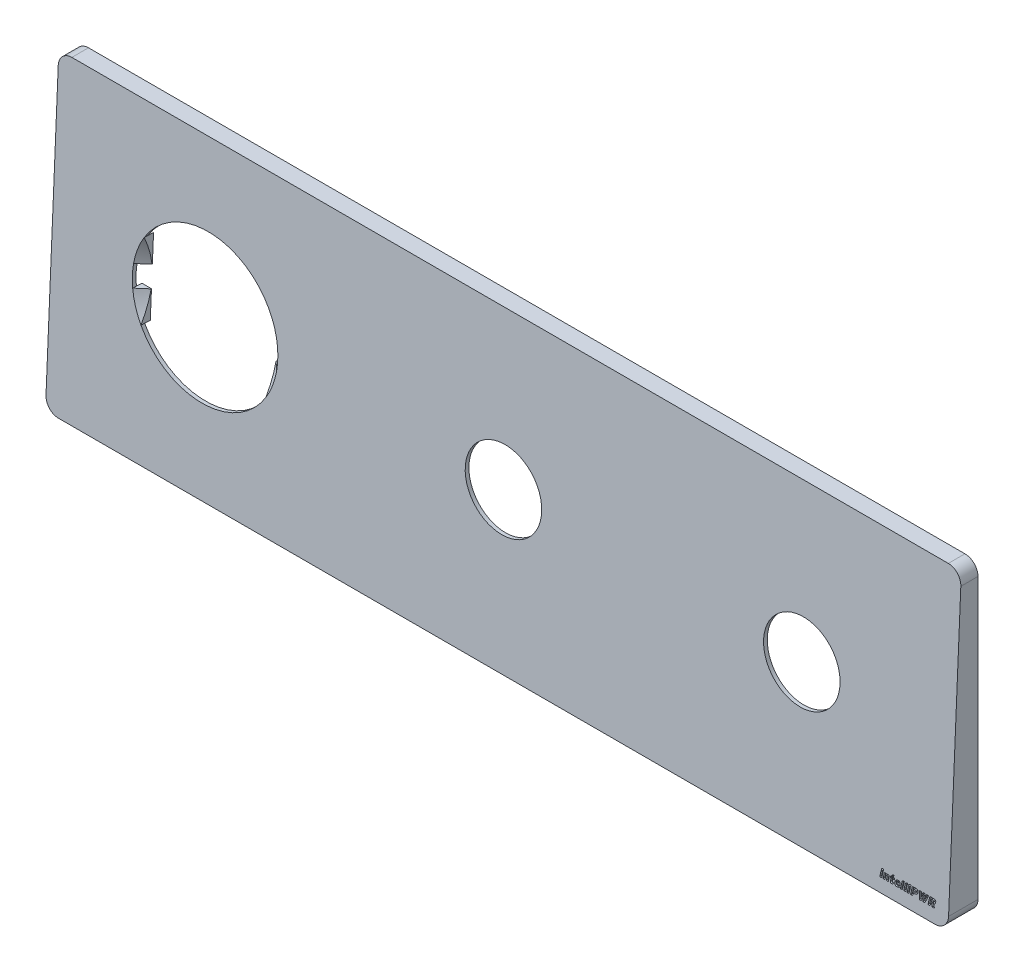
SolidWorks part; units mm, degrees
ref_plane "Front Plane" through (0, 0, 0) normal (0, 0, 1) x (1, 0, 0)
ref_plane "Top Plane" through (0, 0, 0) normal (0, 1, 0) x (1, 0, 0)
ref_plane "Right Plane" through (0, 0, 0) normal (1, 0, 0) x (0, 0, -1)
sketch "Sketch1" plane through (0, 0, 0) normal (0, 0, 1) x (1, 0, 0)
  line L0 (-38.566, 0) -> (72.4153, 0) construction
  line L1 (0, -49.5581) -> (0, 74.5126) construction
  line L2 (-37.5, 40) -> (197.5, 40)
  line L3 (-40, 37.5) -> (-40, -37.5)
  line L4 (-37.5, -40) -> (197.5, -40)
  line L5 (200, 37.5) -> (200, -37.5)
  arc A0 (-40, -37.5) -> (-37.5, -40) centre (-37.5, -37.5) ccw
  arc A1 (197.5, -40) -> (200, -37.5) centre (197.5, -37.5) ccw
  arc A2 (197.5, 40) -> (200, 37.5) centre (197.5, 37.5) cw
  arc A3 (-37.5, 40) -> (-40, 37.5) centre (-37.5, 37.5) ccw
  dimension "D3" = 2.5
  dimension "D1" = 240
  dimension "D2" = 80
  dimension "D4" = 40
  dimension "D5" = 40
extrude "Extrude-Thin1" add sketch "Sketch1" along normal blind 8 thin thin type one direction wall 1
sketch "Sketch5" plane through (201, 0, 0) normal (1, 0, 0) x (0, 0, -1)
  line L0 (20.3178, 0) -> (-25.0092, 0) construction
  line L1 (0, 43.59) -> (0, -45.2443) construction
  line L2 (-3.4562, 41) -> (-8, 41)
  line L3 (-8, 41) -> (-8, -41)
  line L4 (-8, -41) -> (-7.0437, -41)
  line L6 (-7.0437, -41) -> (-3.4562, 41)
  line L7 (-8, -41) -> (0, -41) construction
  line L11 (-8, 41) -> (0, 41) construction
extrude "Cut-Extrude2" cut sketch "Sketch5" against normal blind 242
sketch "Sketch6" plane through (201, 0, 0) normal (1, 0, 0) x (0, 0, -1)
  line L0 (-7.0437, -41) -> (-3.4562, 41)
  line L1 (-3.4562, 41) -> (-4.4572, 41)
  line L2 (-4.4572, 41) -> (-8.0447, -41)
  line L3 (-8.0447, -41) -> (-7.0437, -41)
  line L4 (-3.4562, 41) -> (-3.4562, 45.0301) construction
  dimension "D1" = 1
  dimension "D2" = 90
extrude "Boss-Extrude1" add sketch "Sketch6" against normal blind 242
sketch "Sketch7" plane through (0, 0, 0) normal (0, 0, -1) x (-1, 0, 0)
  line L0 (-201, 37.5) -> (-201, 41)
  line L1 (-201, 41) -> (-197.5, 41)
  line L2 (-18.5365, 0) -> (-146.383, 0) construction
  line L3 (-80, 24.4375) -> (-80, -25.4386) construction
  line L5 (41, 41) -> (37.5, 41)
  line L6 (41, 37.5) -> (41, 41)
  line L7 (41, -37.5) -> (41, -41)
  line L8 (41, -41) -> (37.5, -41)
  line L9 (-201, -41) -> (-197.5, -41)
  line L10 (-201, -37.5) -> (-201, -41)
  arc A0 (-197.5, 41) -> (-201, 37.5) centre (-197.5, 37.5) ccw
  arc A1 (37.5, 41) -> (41, 37.5) centre (37.5, 37.5) cw
  arc A2 (37.5, -41) -> (41, -37.5) centre (37.5, -37.5) ccw
  arc A3 (-197.5, -41) -> (-201, -37.5) centre (-197.5, -37.5) cw
sketch "Sketch8" plane through (0, 0.273, 6.239) normal (0, 0.0437, 0.999) x (1, 0, 0)
  line L0 (0, 0) -> (0, 28.9526) construction
  line L1 (23.1598, 0) -> (-27.4609, 0) construction
  circle A0 centre (0, 0) radius 19.5
  dimension "D1" = 39
extrude "Kes-Ekstrüzyon5" cut sketch "Sketch7" against normal blind 10
extrude "Cut-Extrude3" cut sketch "Sketch8" against normal blind 82
sketch "Sketch9" plane through (0, 0.273, 6.239) normal (0, 0.0437, 0.999) x (1, 0, 0)
  line L1 (182.5318, -37.8124) -> (182.8563, -36.2774)
  line L3 (182.8563, -36.2774) -> (183.3824, -36.2774)
  line L4 (183.3824, -36.2774) -> (183.058, -37.8124)
  line L5 (183.058, -37.8124) -> (182.5318, -37.8124)
  line L6 (184.2906, -37.8124) -> (184.4746, -36.9301)
  line L7 (184.121, -36.9242) -> (183.9366, -37.8124)
  line L8 (183.9366, -37.8124) -> (183.4104, -37.8124)
  line L9 (183.4104, -37.8124) -> (183.7348, -36.2694)
  line L10 (183.7348, -36.2694) -> (184.261, -36.2694)
  line L11 (184.261, -36.2694) -> (184.2407, -36.3734)
  line L12 (185.0186, -36.8721) -> (184.8197, -37.8124)
  line L13 (184.8197, -37.8124) -> (184.2906, -37.8124)
  line L14 (185.3946, -37.3472) -> (185.5346, -36.6755)
  line L15 (185.5346, -36.6755) -> (185.3007, -36.6755)
  line L16 (185.3007, -36.6755) -> (185.3887, -36.2694)
  line L17 (185.3887, -36.2694) -> (185.6226, -36.2694)
  line L18 (185.6226, -36.2694) -> (185.7042, -35.8811)
  line L19 (185.7042, -35.8811) -> (186.2596, -35.6738)
  line L20 (186.2596, -35.6738) -> (186.134, -36.2694)
  line L21 (186.134, -36.2694) -> (186.4673, -36.2694)
  line L22 (186.4673, -36.2694) -> (186.3797, -36.6755)
  line L23 (186.3797, -36.6755) -> (186.0464, -36.6755)
  line L24 (186.0464, -36.6755) -> (185.9292, -37.2389)
  line L25 (186.2571, -37.3099) -> (186.0929, -37.7574)
  line L26 (187.0891, -36.865) -> (187.5277, -36.865)
  line L27 (187.9194, -37.1898) -> (187.0193, -37.1898)
  line L28 (187.6478, -37.3252) -> (187.7794, -37.6631)
  line L29 (188.0814, -37.8124) -> (188.4875, -35.8849)
  line L30 (188.4875, -35.8849) -> (189.0576, -35.6738)
  line L31 (189.0576, -35.6738) -> (188.6076, -37.8124)
  line L32 (188.6076, -37.8124) -> (188.0814, -37.8124)
  line L33 (188.9747, -37.8124) -> (189.3808, -35.8849)
  line L34 (189.3808, -35.8849) -> (189.951, -35.6738)
  line L35 (189.951, -35.6738) -> (189.5009, -37.8124)
  line L36 (189.5009, -37.8124) -> (188.9747, -37.8124)
  line L37 (189.8681, -37.8124) -> (190.1925, -36.2774)
  line L38 (190.1925, -36.2774) -> (190.7187, -36.2774)
  line L39 (190.7187, -36.2774) -> (190.3943, -37.8124)
  line L40 (190.3943, -37.8124) -> (189.8681, -37.8124)
  line L41 (191.9923, -36.2152) -> (191.6852, -36.2152)
  line L42 (191.6852, -36.2152) -> (191.5858, -36.6755)
  line L43 (191.5858, -36.6755) -> (191.884, -36.6755)
  line L44 (191.7728, -37.1357) -> (191.4894, -37.1357)
  line L45 (191.4894, -37.1357) -> (191.3489, -37.8124)
  line L46 (191.3489, -37.8124) -> (190.7906, -37.8124)
  line L47 (190.7906, -37.8124) -> (191.2233, -35.755)
  line L48 (191.2233, -35.755) -> (192.1031, -35.755)
  line L49 (194.6592, -37.8124) -> (194.1292, -37.8124)
  line L50 (194.1292, -37.8124) -> (194.1292, -37.3658)
  line L51 (193.8492, -37.3658) -> (193.6618, -37.8124)
  line L52 (193.6618, -37.8124) -> (193.1445, -37.8124)
  line L53 (193.1445, -37.8124) -> (193.0891, -35.755)
  line L54 (193.0891, -35.755) -> (193.6737, -35.755)
  line L55 (193.6737, -35.755) -> (193.6563, -36.0989)
  line L56 (193.9309, -36.1019) -> (194.0742, -35.755)
  line L57 (194.0742, -35.755) -> (194.6004, -35.755)
  line L58 (194.6004, -35.755) -> (194.5975, -36.1019)
  line L59 (194.8724, -36.0989) -> (195.001, -35.755)
  line L60 (195.001, -35.755) -> (195.5801, -35.755)
  line L61 (195.5801, -35.755) -> (194.6592, -37.8124)
  line L62 (196.7107, -36.2152) -> (196.3685, -36.2152)
  line L63 (196.3685, -36.2152) -> (196.2721, -36.6755)
  line L64 (196.2721, -36.6755) -> (196.6054, -36.6755)
  line L65 (196.5935, -37.8124) -> (196.4066, -37.1357)
  line L66 (196.4066, -37.1357) -> (196.1786, -37.1357)
  line L67 (196.1786, -37.1357) -> (196.0322, -37.8124)
  line L68 (196.0322, -37.8124) -> (195.4739, -37.8124)
  line L69 (195.4739, -37.8124) -> (195.9066, -35.755)
  line L70 (195.9066, -35.755) -> (196.8215, -35.755)
  line L71 (196.9823, -37.0278) -> (197.228, -37.8124)
  line L72 (197.228, -37.8124) -> (196.5935, -37.8124)
  spline S0 degree 3 poles (183.5051, -35.901) (183.4969, -35.9395) (183.475, -35.9951) (183.4259, -36.0567) (183.38, -36.0941) (183.3281, -36.1243) (183.2494, -36.1531) (183.1859, -36.1615) (183.1426, -36.1611) knots 0 0 0 0 0.243996 0.362518 0.483924 0.60781 0.732572 1 1 1 1
  spline S1 degree 3 poles (183.1426, -36.1611) (183.1034, -36.1614) (183.0464, -36.1543) (182.9794, -36.1247) (182.9459, -36.0992) (182.9246, -36.0749) (182.9109, -36.0553) (182.9015, -36.0333) (182.894, -36.0101) (182.8904, -35.985) (182.8893, -35.9483) (182.8933, -35.92) (182.8973, -35.901) knots 0 0 0 0 0.278361 0.398909 0.514848 0.572098 0.627439 0.683254 0.740687 0.799243 0.862128 1 1 1 1
  spline S2 degree 3 poles (182.8973, -35.901) (182.9046, -35.8648) (182.9269, -35.8129) (182.975, -35.7545) (183.0208, -35.7171) (183.0729, -35.6861) (183.1494, -35.6544) (183.2122, -35.6474) (183.2539, -35.6468) knots 0 0 0 0 0.233169 0.351346 0.477078 0.606225 0.734605 1 1 1 1
  spline S3 degree 3 poles (183.2539, -35.6468) (183.294, -35.6476) (183.3536, -35.6526) (183.4215, -35.6852) (183.4549, -35.7118) (183.4756, -35.7369) (183.4893, -35.7563) (183.4986, -35.7777) (183.5062, -35.8) (183.5103, -35.8237) (183.5118, -35.8577) (183.5094, -35.8837) (183.5051, -35.901) knots 0 0 0 0 0.289932 0.415109 0.533191 0.591068 0.646913 0.702321 0.757398 0.814668 0.873138 1 1 1 1
  spline S4 degree 3 poles (184.4746, -36.9301) (184.4788, -36.907) (184.4857, -36.8741) (184.4892, -36.8319) (184.4898, -36.805) (184.4882, -36.7812) (184.4845, -36.7603) (184.4788, -36.7423) (184.4679, -36.723) (184.4497, -36.7035) (184.4108, -36.6804) (184.3757, -36.6755) (184.3519, -36.6755) knots 0 0 0 0 0.206248 0.294568 0.372668 0.442258 0.50401 0.558886 0.607164 0.698385 0.78958 1 1 1 1
  spline S5 degree 3 poles (184.3519, -36.6755) (184.3255, -36.6748) (184.2865, -36.6813) (184.2396, -36.7028) (184.2139, -36.7214) (184.195, -36.7398) (184.1826, -36.7576) (184.1702, -36.7778) (184.159, -36.8014) (184.1478, -36.8274) (184.1346, -36.8686) (184.1258, -36.9012) (184.121, -36.9242) knots 0 0 0 0 0.211446 0.310999 0.411311 0.464021 0.521401 0.584742 0.653943 0.729878 0.812026 1 1 1 1
  spline S6 degree 3 poles (184.2407, -36.3734) (184.298, -36.3381) (184.3731, -36.2966) (184.4716, -36.2624) (184.5492, -36.2465) (184.6106, -36.2424) (184.6531, -36.2423) knots 0 0 0 0 0.460544 0.581348 0.71025 1 1 1 1
  spline S7 degree 3 poles (184.6531, -36.2423) (184.6921, -36.2424) (184.7488, -36.2462) (184.8195, -36.2639) (184.8654, -36.2813) (184.9061, -36.3046) (184.9414, -36.333) (184.9715, -36.3666) (184.9962, -36.4051) (185.0154, -36.4485) (185.031, -36.4959) (185.0401, -36.5481) (185.0459, -36.6044) (185.0457, -36.6652) (185.0409, -36.7555) (185.0276, -36.8247) (185.0186, -36.8721) knots 0 0 0 0 0.133988 0.193276 0.249258 0.301629 0.353161 0.403793 0.455519 0.509135 0.565969 0.625946 0.690505 0.759591 0.834116 1 1 1 1
  spline S8 degree 3 poles (186.0929, -37.7574) (186.0333, -37.7837) (185.9543, -37.8089) (185.856, -37.8278) (185.7854, -37.8368) (185.7316, -37.8398) (185.6953, -37.8395) knots 0 0 0 0 0.477931 0.605354 0.733676 1 1 1 1
  spline S9 degree 3 poles (185.6953, -37.8395) (185.6631, -37.8397) (185.6164, -37.8366) (185.5579, -37.8244) (185.5198, -37.8123) (185.4862, -37.7963) (185.457, -37.7764) (185.4315, -37.7536) (185.4109, -37.7263) (185.3947, -37.6948) (185.3825, -37.6588) (185.3741, -37.6184) (185.3701, -37.5731) (185.3704, -37.5232) (185.3757, -37.4469) (185.3864, -37.3879) (185.3946, -37.3472) knots 0 0 0 0 0.137072 0.197692 0.25376 0.30627 0.355446 0.403354 0.450795 0.500091 0.55332 0.611471 0.675246 0.745926 0.823384 1 1 1 1
  spline S10 degree 3 poles (185.9292, -37.2389) (185.9236, -37.2632) (185.9182, -37.2972) (185.9231, -37.3387) (185.9338, -37.3601) (185.9509, -37.3746) (185.9818, -37.3894) (186.0096, -37.391) (186.0286, -37.3916) knots 0 0 0 0 0.332431 0.451864 0.549009 0.641836 0.743993 1 1 1 1
  spline S11 degree 3 poles (186.0286, -37.3916) (186.0648, -37.392) (186.1102, -37.3818) (186.1624, -37.3596) (186.204, -37.3401) (186.2353, -37.3223) (186.2571, -37.3099) knots 0 0 0 0 0.439023 0.560347 0.693744 1 1 1 1
  spline S12 degree 3 poles (187.5277, -36.865) (187.5293, -36.8295) (187.529, -36.7789) (187.5142, -36.7178) (187.5009, -36.6876) (187.4872, -36.6673) (187.4736, -36.6552) (187.4583, -36.6443) (187.44, -36.6359) (187.4195, -36.6292) (187.3871, -36.6229) (187.3615, -36.621) (187.3437, -36.6213) knots 0 0 0 0 0.296749 0.416695 0.521302 0.57019 0.620056 0.671542 0.726187 0.786738 0.851475 1 1 1 1
  spline S13 degree 3 poles (187.3437, -36.6213) (187.3155, -36.6212) (187.2732, -36.6284) (187.2232, -36.6548) (187.1894, -36.682) (187.1587, -36.7168) (187.1208, -36.7764) (187.1008, -36.8283) (187.0891, -36.865) knots 0 0 0 0 0.222963 0.331063 0.443598 0.564297 0.695588 1 1 1 1
  spline S14 degree 3 poles (187.946, -37.0879) (187.9408, -37.1068) (187.9333, -37.1411) (187.9259, -37.1755) (187.9194, -37.1898) knots 0 0 0 0 0.556454 1 1 1 1
  spline S15 degree 3 poles (187.0193, -37.1898) (187.0159, -37.2265) (187.016, -37.2792) (187.0367, -37.342) (187.0613, -37.3767) (187.0938, -37.4024) (187.1478, -37.4284) (187.1948, -37.4328) (187.2265, -37.4334) knots 0 0 0 0 0.296056 0.414656 0.524028 0.631631 0.743271 1 1 1 1
  spline S16 degree 3 poles (187.2265, -37.4334) (187.2603, -37.4332) (187.3107, -37.4303) (187.3768, -37.4199) (187.4263, -37.4095) (187.477, -37.3938) (187.5522, -37.3685) (187.6086, -37.3424) (187.6478, -37.3252) knots 0 0 0 0 0.230948 0.344109 0.457558 0.576208 0.706686 1 1 1 1
  spline S17 degree 3 poles (187.7794, -37.6631) (187.7271, -37.6911) (187.6473, -37.7284) (187.5385, -37.7689) (187.4578, -37.7948) (187.3756, -37.8147) (187.2619, -37.8343) (187.1745, -37.8392) (187.1157, -37.8395) knots 0 0 0 0 0.256454 0.380104 0.501569 0.622664 0.745735 1 1 1 1
  spline S18 degree 3 poles (187.1157, -37.8395) (187.0622, -37.8393) (186.9842, -37.8333) (186.8864, -37.8083) (186.822, -37.7829) (186.7641, -37.7507) (186.7129, -37.7122) (186.6679, -37.6684) (186.6299, -37.6183) (186.5991, -37.5624) (186.5744, -37.5016) (186.5568, -37.4353) (186.5454, -37.3642) (186.541, -37.2886) (186.5441, -37.1801) (186.5568, -37.0976) (186.5688, -37.0422) knots 0 0 0 0 0.139839 0.202933 0.262718 0.320042 0.375234 0.429353 0.483442 0.538621 0.595401 0.654489 0.717096 0.783083 0.851913 1 1 1 1
  spline S19 degree 3 poles (186.5688, -37.0422) (186.5831, -36.9792) (186.6085, -36.8876) (186.6551, -36.7729) (186.6947, -36.6953) (186.7382, -36.6235) (186.786, -36.5578) (186.8379, -36.4981) (186.8939, -36.4448) (186.9531, -36.3973) (187.0154, -36.3562) (187.0807, -36.3212) (187.1487, -36.2925) (187.2191, -36.2701) (187.3158, -36.2482) (187.3903, -36.2428) (187.4401, -36.2423) knots 0 0 0 0 0.150666 0.221012 0.288513 0.353593 0.416668 0.477731 0.537737 0.596692 0.654605 0.711686 0.769156 0.826457 0.883737 1 1 1 1
  spline S20 degree 3 poles (187.4401, -36.2423) (187.4892, -36.2427) (187.5612, -36.2476) (187.6515, -36.2705) (187.712, -36.293) (187.7667, -36.323) (187.816, -36.3594) (187.8597, -36.4023) (187.8978, -36.4519) (187.9292, -36.5083) (187.954, -36.5714) (187.9704, -36.6415) (187.9806, -36.718) (187.9827, -36.8011) (187.9759, -36.9259) (187.96, -37.022) (187.946, -37.0879) knots 0 0 0 0 0.125235 0.182282 0.236835 0.289224 0.340575 0.392377 0.44488 0.49922 0.556302 0.616919 0.682128 0.752543 0.828415 1 1 1 1
  spline S21 degree 3 poles (190.8414, -35.901) (190.8332, -35.9395) (190.8113, -35.9951) (190.7621, -36.0567) (190.7163, -36.0941) (190.6643, -36.1243) (190.5857, -36.1531) (190.5221, -36.1615) (190.4789, -36.1611) knots 0 0 0 0 0.243996 0.362518 0.483924 0.60781 0.732572 1 1 1 1
  spline S22 degree 3 poles (190.4789, -36.1611) (190.4396, -36.1614) (190.3826, -36.1543) (190.3156, -36.1247) (190.2822, -36.0992) (190.2609, -36.0749) (190.2472, -36.0553) (190.2378, -36.0333) (190.2303, -36.0101) (190.2266, -35.985) (190.2256, -35.9483) (190.2295, -35.92) (190.2335, -35.901) knots 0 0 0 0 0.278361 0.398909 0.514848 0.572098 0.627439 0.683254 0.740687 0.799243 0.862128 1 1 1 1
  spline S23 degree 3 poles (190.2335, -35.901) (190.2409, -35.8648) (190.2632, -35.8129) (190.3113, -35.7545) (190.3571, -35.7171) (190.4091, -35.6861) (190.4857, -35.6544) (190.5484, -35.6474) (190.5901, -35.6468) knots 0 0 0 0 0.233169 0.351346 0.477078 0.606225 0.734605 1 1 1 1
  spline S24 degree 3 poles (190.5901, -35.6468) (190.6303, -35.6476) (190.6899, -35.6526) (190.7578, -35.6852) (190.7912, -35.7118) (190.8118, -35.7369) (190.8255, -35.7563) (190.8349, -35.7777) (190.8425, -35.8) (190.8465, -35.8237) (190.8481, -35.8577) (190.8456, -35.8837) (190.8414, -35.901) knots 0 0 0 0 0.289932 0.415109 0.533191 0.591068 0.646913 0.702321 0.757398 0.814668 0.873138 1 1 1 1
  spline S25 degree 3 poles (192.1911, -36.4411) (192.1981, -36.411) (192.2031, -36.3661) (192.1907, -36.3103) (192.176, -36.2817) (192.16, -36.2619) (192.1446, -36.2493) (192.1264, -36.2386) (192.1054, -36.2297) (192.081, -36.2237) (192.0434, -36.2164) (192.0132, -36.2152) (191.9923, -36.2152) knots 0 0 0 0 0.254138 0.360693 0.463314 0.514097 0.568127 0.624482 0.687009 0.753851 0.828928 1 1 1 1
  spline S26 degree 3 poles (191.884, -36.6755) (191.9253, -36.6752) (191.9847, -36.6702) (192.0552, -36.6447) (192.0969, -36.6188) (192.1302, -36.5843) (192.1679, -36.5274) (192.184, -36.4765) (192.1911, -36.4411) knots 0 0 0 0 0.29062 0.412092 0.523259 0.631698 0.74585 1 1 1 1
  spline S27 degree 3 poles (192.7583, -36.4322) (192.745, -36.4934) (192.7207, -36.5823) (192.6705, -36.6906) (192.6282, -36.7622) (192.5799, -36.8261) (192.5278, -36.8845) (192.4699, -36.9355) (192.4079, -36.9809) (192.3411, -37.0191) (192.2706, -37.0524) (192.1959, -37.0794) (192.1174, -37.1003) (192.0356, -37.1165) (191.9205, -37.1307) (191.8324, -37.1365) (191.7728, -37.1357) knots 0 0 0 0 0.141358 0.206507 0.268664 0.328624 0.386922 0.444795 0.502156 0.559848 0.618159 0.677698 0.738624 0.801161 0.865596 1 1 1 1
  spline S28 degree 3 poles (192.1031, -35.755) (192.1595, -35.7545) (192.242, -35.7594) (192.3481, -35.7746) (192.4205, -35.7906) (192.4878, -35.8108) (192.5484, -35.8376) (192.6029, -35.8692) (192.6503, -35.9073) (192.6911, -35.9508) (192.7246, -36.0007) (192.7504, -36.057) (192.7685, -36.1196) (192.7791, -36.1885) (192.7814, -36.2941) (192.7698, -36.3761) (192.7583, -36.4322) knots 0 0 0 0 0.148313 0.216935 0.281917 0.343283 0.401251 0.455966 0.508744 0.560452 0.612308 0.666251 0.722712 0.783153 0.849211 1 1 1 1
  spline S29 degree 3 poles (194.1292, -37.3658) (194.1269, -37.284) (194.1283, -37.1605) (194.1355, -36.9976) (194.1408, -36.8793) (194.1467, -36.7691) (194.1519, -36.6833) (194.1555, -36.6211) (194.1605, -36.5706) (194.1642, -36.5352) (194.1677, -36.5134) knots 0 0 0 0 0.287418 0.433707 0.573086 0.703583 0.821712 0.874842 0.922617 1 1 1 1
  spline S30 degree 3 poles (194.1677, -36.5134) (194.1615, -36.5355) (194.1493, -36.5706) (194.134, -36.6213) (194.119, -36.6661) (194.1033, -36.7149) (194.0853, -36.7666) (194.0661, -36.821) (194.0373, -36.8977) (193.9988, -36.9979) (193.9339, -37.161) (193.8835, -37.2843) (193.8492, -37.3658) knots 0 0 0 0 0.075538 0.122272 0.174583 0.231301 0.291254 0.354892 0.421349 0.561229 0.70869 1 1 1 1
  spline S31 degree 3 poles (193.6563, -36.0989) (193.6542, -36.175) (193.6483, -36.2905) (193.6383, -36.4452) (193.6297, -36.5627) (193.6213, -36.6781) (193.6078, -36.821) (193.5985, -36.9253) (193.5916, -36.9923) knots 0 0 0 0 0.254779 0.387257 0.519329 0.649082 0.774717 1 1 1 1
  spline S32 degree 3 poles (193.5916, -36.9923) (193.6117, -36.9251) (193.6463, -36.8211) (193.6993, -36.6803) (193.744, -36.5665) (193.7913, -36.4507) (193.852, -36.2948) (193.8989, -36.1785) (193.9309, -36.1019) knots 0 0 0 0 0.22063 0.344767 0.473491 0.605508 0.738598 1 1 1 1
  spline S33 degree 3 poles (194.5975, -36.1019) (194.5952, -36.1789) (194.5937, -36.2952) (194.5917, -36.4504) (194.5893, -36.5668) (194.5853, -36.6807) (194.577, -36.8224) (194.5688, -36.9258) (194.5624, -36.9923) knots 0 0 0 0 0.259139 0.391547 0.522548 0.65076 0.77529 1 1 1 1
  spline S34 degree 3 poles (194.5624, -36.9923) (194.5824, -36.925) (194.6152, -36.8204) (194.6635, -36.6779) (194.7028, -36.5624) (194.745, -36.445) (194.8026, -36.2905) (194.8461, -36.1755) (194.8724, -36.0989) knots 0 0 0 0 0.222644 0.347664 0.477214 0.609762 0.743344 1 1 1 1
  spline S35 degree 3 poles (196.9121, -36.4407) (196.9178, -36.4114) (196.9227, -36.367) (196.9079, -36.3124) (196.8932, -36.2833) (196.8767, -36.2633) (196.8615, -36.25) (196.8427, -36.2398) (196.822, -36.23) (196.7979, -36.2237) (196.7609, -36.2165) (196.7312, -36.2152) (196.7107, -36.2152) knots 0 0 0 0 0.248425 0.356514 0.461365 0.51411 0.56924 0.626959 0.689289 0.756874 0.831295 1 1 1 1
  spline S36 degree 3 poles (196.6054, -36.6755) (196.6467, -36.6753) (196.706, -36.6701) (196.7764, -36.6438) (196.8177, -36.617) (196.8513, -36.5826) (196.8886, -36.5258) (196.9046, -36.4756) (196.9121, -36.4407) knots 0 0 0 0 0.291424 0.412585 0.525066 0.635143 0.748168 1 1 1 1
  spline S37 degree 3 poles (196.8215, -35.755) (196.8779, -35.7545) (196.9604, -35.7593) (197.0665, -35.7746) (197.139, -35.7905) (197.206, -35.8114) (197.2669, -35.8375) (197.3212, -35.8693) (197.3687, -35.907) (197.41, -35.9497) (197.4431, -35.9994) (197.4698, -36.0545) (197.4882, -36.1161) (197.4992, -36.1841) (197.5021, -36.2884) (197.4911, -36.3696) (197.4793, -36.425) knots 0 0 0 0 0.149106 0.218094 0.283424 0.345229 0.403358 0.458364 0.511193 0.563161 0.614984 0.668363 0.724518 0.784604 0.849908 1 1 1 1
  spline S38 degree 3 poles (197.4793, -36.425) (197.4711, -36.4624) (197.4574, -36.5173) (197.4311, -36.5868) (197.4103, -36.6359) (197.3866, -36.6821) (197.36, -36.7255) (197.3315, -36.7666) (197.2897, -36.8171) (197.2324, -36.8747) (197.1299, -36.9558) (197.0433, -37.0031) (196.9823, -37.0278) knots 0 0 0 0 0.140675 0.207617 0.273118 0.336662 0.398558 0.459984 0.520403 0.639569 0.758048 1 1 1 1
extrude "Cut-Extrude13" cut sketch "Sketch9" against normal blind 0.5
sketch "Çizim2" plane through (0, 0.273, 6.239) normal (0, 0.0437, 0.999) x (1, 0, 0)
  line L0 (0, 29.0101) -> (0, -24.8666) construction
  line L1 (29.1526, 0) -> (-30.9953, 0) construction
  line L2 (19.2979, 2.8) -> (16.75, 2.8)
  line L3 (16.75, 9.9844) -> (16.75, 2.8)
  line L4 (16.75, -9.9844) -> (16.75, -2.8)
  line L5 (-19.2979, 2.8) -> (-16.75, 2.8)
  line L6 (-16.75, 9.9844) -> (-16.75, 2.8)
  line L7 (19.2979, -2.8) -> (16.75, -2.8)
  line L8 (-16.75, -9.9844) -> (-16.75, -2.8)
  line L9 (-19.2979, -2.8) -> (-16.75, -2.8)
  circle A0 centre (0, 0) radius 19.5
  dimension "D2" = 39
  dimension "D1" = 33.5
  dimension "D3" = 5.6
extrude "Yükseklik-Ekstrüzyon1" add sketch "Çizim2" against normal blind 2.5 contours L6 A0 L5 | L9 A0 L8 | L2 A0 L3 | L4 A0 L7
sketch "Çizim3" plane through (0, 0.273, 6.239) normal (0, 0.0437, 0.999) x (1, 0, 0)
  line L0 (0, 0) -> (59.8558, 0) construction
ref_plane "Düzlem1" through (0, 0, 0) normal (0, -0.999, 0.0437) x (-1, 0, 0)
sketch "Çizim4" plane through (0, 0, 0) normal (0, -0.999, 0.0437) x (-1, 0, 0)
  line L0 (0, 22.8886) -> (0, -30.2322) construction
  line L1 (-50.2148, -6.245) -> (60.571, -6.245) construction
  line L3 (19.5, -6.245) -> (16.9, -3.745)
  line L4 (16.9, -3.745) -> (16.9, -6.245)
  line L5 (16.9, -6.245) -> (19.5, -6.245)
  dimension "D1" = 19.5
  dimension "D2" = 2.5
  dimension "D3" = 2.6
revolve "Kes-Döndür2" cut sketch "Çizim4" angle 360 about L0
ref_plane "Düzlem2" through (0, 0, 0) normal (0, 0, -1) x (-1, 0, 0)
sketch "Çizim7" plane through (0, 0, 0) normal (0, 0, -1) x (-1, 0, 0)
  line L0 (0, 0) -> (0, -25.6736) construction
  line L1 (0, 0) -> (31.3225, 0) construction
  line L2 (37.5, -41) -> (-197.5, -41) construction
  line L4 (41, 37.5) -> (41, -37.5) construction
  line L5 (-80, 56.4569) -> (-80, -76.9241) construction
  line L6 (-160, 60.597) -> (-160, -76.9241) construction
  circle A0 centre (29, -29) radius 5
  circle A1 centre (29, 29) radius 5
  circle A2 centre (-29, -29) radius 5
  circle A3 centre (-29, 29) radius 5
  circle A4 centre (-51, -29) radius 5
  circle A5 centre (-109, -29) radius 5
  circle A6 centre (-131, -29) radius 5
  circle A7 centre (-189, -29) radius 5
  circle A8 centre (-51, 29) radius 5
  circle A9 centre (-109, 29) radius 5
  circle A10 centre (-131, 29) radius 5
  circle A11 centre (-189, 29) radius 5
  dimension "D3" = 10
  dimension "D4" = 10
  dimension "D5" = 12
  dimension "D6" = 29
  dimension "D7" = 10
  dimension "D8" = 12
  dimension "D1" = 12
  dimension "D2" = 12
  dimension "D9" = 29
extrude "Yükseklik-Ekstrüzyon4" add sketch "Çizim7" against normal up to body
sketch "Çizim10" plane through (0, -41, 0) normal (0, -1, 0) x (1, 0, 0)
  line L0 (0, 0) -> (0, 11.0435) construction
  line L1 (0, 0) -> (37.9352, 0) construction
  line L5 (16.4791, 4.3882) -> (-16.4791, 4.3882)
  line L6 (-22, 0) -> (22, 0)
  line L7 (-22, 0) -> (-18.6341, 3.4753)
  line L8 (22, 0) -> (18.6341, 3.4753)
  arc A2 (18.6341, 3.4753) -> (16.4791, 4.3882) centre (16.4791, 1.3882) ccw
  arc A3 (-18.6341, 3.4753) -> (-16.4791, 4.3882) centre (-16.4791, 1.3882) cw
  point P20 (0, 0)
  point P21 (0, 4.3882)
extrude "Kes-Ekstrüzyon2" cut sketch "Çizim10" against normal blind 3
sketch "Çizim18" plane through (0, 0, 0) normal (0, 0, -1) x (-1, 0, 0)
  line L1 (-194, 34) -> (34, 34)
  line L2 (-194, 34) -> (-194, -34)
  line L3 (-194, -34) -> (34, -34)
  line L4 (34, 34) -> (34, -34)
  circle A0 centre (29, 29) radius 5 construction
  circle A1 centre (-51, 29) radius 5 construction
  circle A2 centre (-51, -29) radius 5 construction
  circle A3 centre (-189, -29) radius 5 construction
extrude "Kes-Ekstrüzyon8" cut sketch "Çizim18" against normal blind 1.5
sketch "Çizim19" plane through (0, 0, 1.5) normal (0, 0, -1) x (-1, 0, 0)
  line L0 (0, 0) -> (-168.1209, 0) construction
  circle A0 centre (-189, 29) radius 1.55
  circle A1 centre (-109, 29) radius 1.55
  circle A2 centre (-29, 29) radius 1.55
  circle A3 centre (29, 29) radius 1.55
  circle A4 centre (29, -29) radius 1.55
  circle A5 centre (-29, -29) radius 1.55
  circle A6 centre (-51, 29) radius 1.55
  circle A7 centre (-131, 29) radius 1.55
  circle A8 centre (-131, -29) radius 1.55
  circle A9 centre (-51, -29) radius 1.55
  circle A10 centre (-29, -29) radius 1.55
  circle A11 centre (-109, -29) radius 1.55
  circle A12 centre (-189, -29) radius 1.55
  dimension "D1" = 3.1
  dimension "D2" = 3.1
  dimension "D3" = 3.1
  dimension "D5" = 3.1
  dimension "D6" = 3.1
  dimension "D4" = 4
extrude "Kes-Ekstrüzyon10" cut sketch "Çizim19" against normal blind 2 contours A0 | A7 | A1 | A8 | A11 | A12 | A9 | A5 | A4 | A2 | A3 | A6
sketch "Çizim20" plane through (0, 0.273, 6.239) normal (0, 0.0437, 0.999) x (1, 0, 0)
  line L0 (80, 63.7441) -> (80, -67.8447) construction
  line L1 (160, 63.7441) -> (160, -67.8447) construction
  line L4 (0, 0) -> (184.2214, 0) construction
  circle A0 centre (80, 0) radius 10.25
  circle A1 centre (160, 0) radius 10.25
  dimension "D1" = 20.5
  dimension "D2" = 20.5
extrude "Kes-Ekstrüzyon11" cut sketch "Çizim20" against normal blind 2
